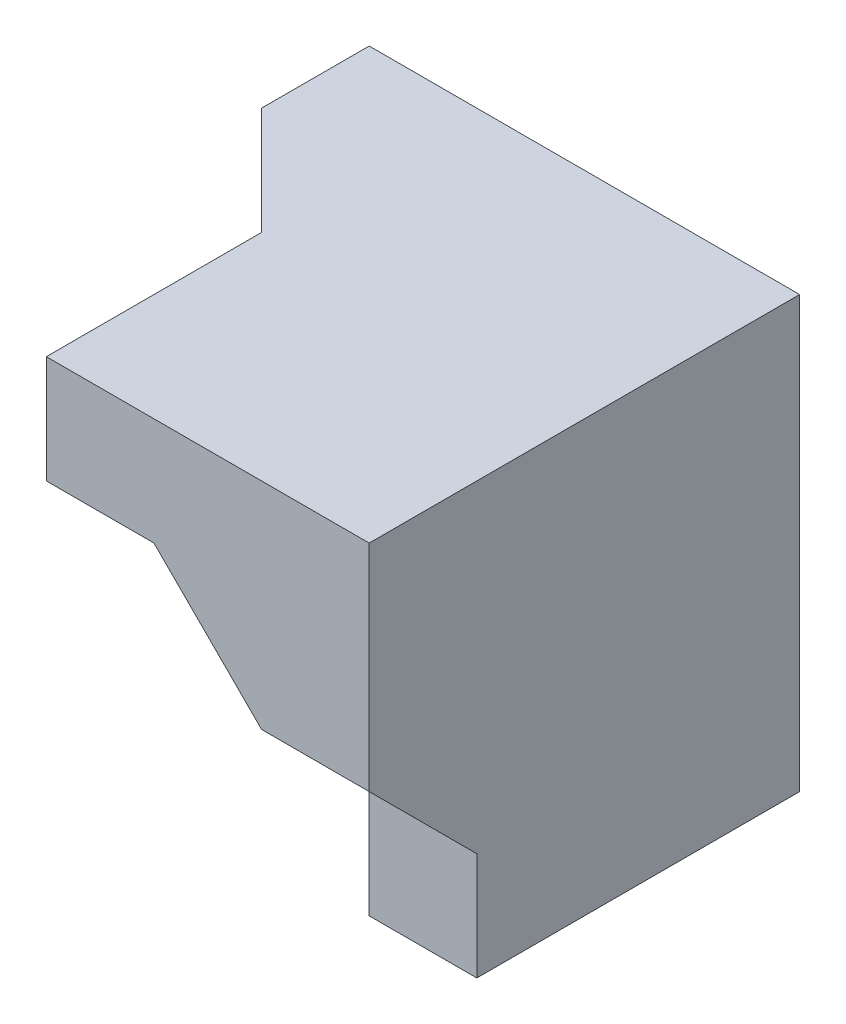
SolidWorks part; units mm, degrees
ref_plane "Front Plane" through (0, 0, 0) normal (0, 0, 1) x (1, 0, 0)
ref_plane "Top Plane" through (0, 0, 0) normal (0, 1, 0) x (1, 0, 0)
ref_plane "Right Plane" through (0, 0, 0) normal (1, 0, 0) x (0, 0, -1)
sketch "Sketch1" plane through (0, 0, 0) normal (0, 0, 1) x (1, 0, 0)
  line L1 (0, 0) -> (40, 0)
  line L2 (0, 0) -> (0, 40)
  line L3 (0, 40) -> (40, 40)
  line L4 (40, 0) -> (40, 40)
  dimension "D1" = 40
  dimension "D2" = 40
extrude "Boss-Extrude1" add sketch "Sketch1" along normal blind 20
sketch "Sketch2" plane through (40, 0, 0) normal (1, 0, 0) x (0, 0, -1)
  line L0 (-20, 0) -> (-30, 0)
  line L1 (-30, 0) -> (-30, 10)
  line L2 (-30, 10) -> (-20, 0)
  line L3 (-20, 0) -> (-20, 10)
  line L4 (-20, 0) -> (-20, 40) construction
  line L5 (-30, 10) -> (-20, 10)
  dimension "D1" = 10
  dimension "D2" = 10
extrude "Boss-Extrude3" add sketch "Sketch2" against normal blind 10 separate body contours L2 L1 L0
sketch "Sketch3" plane through (40, 0, 0) normal (1, 0, 0) x (0, 0, -1)
  line L0 (-20, 0) -> (-20, 10)
  line L1 (-20, 40) -> (-30, 40)
  line L2 (-20, 40) -> (-20, 10)
  line L3 (-20, 10) -> (-30, 10)
  line L4 (-30, 40) -> (-30, 10)
  line L5 (-20, 10) -> (-30, 10)
  line L6 (-30, 10) -> (-20, 0)
  line M3 (-20, 40) -> (-20, 0)
extrude "Boss-Extrude5" add sketch "Sketch3" against normal blind 10 contours L1 L4 L3 M3
sketch "Sketch4" plane through (40, 0, 0) normal (1, 0, 0) x (0, 0, -1)
  line L0 (-20, 0) -> (-20, 10)
  line L1 (-20, 10) -> (-30, 10)
  line L2 (-30, 10) -> (-20, 0)
extrude "Boss-Extrude6" add sketch "Sketch4" against normal blind 10
sketch "Sketch5" plane through (0, 0, 20) normal (0, 0, 1) x (1, 0, 0)
  line L0 (0, 0) -> (30, 0) construction
  line L1 (0, 40) -> (10, 40)
  line L2 (0, 40) -> (0, 0)
  line L3 (0, 0) -> (10, 0)
  line L4 (10, 40) -> (10, 0)
  dimension "D1" = 10
extrude "Cut-Extrude3" cut sketch "Sketch5" against normal blind 25
sketch "Sketch7" plane through (0, 0, 20) normal (0, 0, 1) x (1, 0, 0)
  line L0 (10, 10) -> (20, 0)
  line L1 (10, 0) -> (10, 40) construction
  line L2 (10, 0) -> (30, 0) construction
  line L3 (20, 0) -> (10, 0)
  line L4 (10, 0) -> (10, 10)
  dimension "D1" = 10
  dimension "D2" = 10
extrude "Cut-Extrude4" cut sketch "Sketch7" against normal blind 25
sketch "Sketch8" plane through (0, 0, 20) normal (0, 0, 1) x (1, 0, 0)
  line L0 (30, 0) -> (10, 20)
  line L1 (10, 10) -> (10, 40) construction
  line L2 (10, 20) -> (10, 10)
  line L3 (10, 10) -> (20, 0)
  line L4 (20, 0) -> (30, 0)
  dimension "D1" = 20
extrude "Cut-Extrude5" cut sketch "Sketch8" against normal blind 10
sketch "Sketch9" plane through (10, 0, 0) normal (-1, 0, 0) x (0, 0, 1)
  line L0 (0, 40) -> (0, 10) construction
  line L1 (20, 40) -> (0, 40)
  line L2 (20, 40) -> (20, 20)
  line L3 (20, 20) -> (0, 20)
  line L4 (0, 40) -> (0, 20)
  dimension "D1" = 20
extrude "Boss-Extrude7" add sketch "Sketch9" along normal blind 10
sketch "Sketch10" plane through (0, 40, 0) normal (0, 1, 0) x (1, 0, 0)
  line L0 (10, -20) -> (0, -10)
  line L1 (30, -20) -> (0, -20) construction
  line L2 (0, -20) -> (0, 0) construction
  line L3 (0, -10) -> (0, -20)
  line L4 (0, -20) -> (10, -20)
  dimension "D1" = 10
  dimension "D2" = 10
extrude "Cut-Extrude6" cut sketch "Sketch10" against normal blind 10
sketch "Sketch11" plane through (30, 0, 0) normal (-1, 0, 0) x (0, 0, 1)
  line L0 (30, 10) -> (40, 20)
  line L1 (30, 0) -> (30, 40) construction
  line L2 (40, 20) -> (40, 40)
  line L3 (40, 40) -> (30, 40)
  line L8 (30, 0) -> (30, 40)
  line L9 (30, 40) -> (20, 40)
  line L10 (20, 40) -> (20, 0)
  line L11 (20, 0) -> (30, 0)
  line L12 (30, 10) -> (30, 40)
  dimension "D1" = 10
  dimension "D2" = 10
  dimension "D3" = 10
  dimension "D4" = 0
extrude "Boss-Extrude8" add sketch "Sketch11" against normal blind 10
sketch "Sketch12" plane through (30, 0, 0) normal (-1, 0, 0) x (0, 0, 1)
  line L0 (20, 0) -> (20, 40) construction
  line L1 (40, 40) -> (20, 40)
  line L2 (40, 40) -> (40, 30)
  line L3 (40, 30) -> (20, 30)
  line L4 (20, 40) -> (20, 30)
  dimension "D1" = 10
extrude "Boss-Extrude9" add sketch "Sketch12" along normal blind 20
sketch "Sketch13" plane through (0, 0, 40) normal (0, 0, 1) x (1, 0, 0)
  line L0 (30, 20) -> (20, 30)
  line L1 (10, 30) -> (30, 30) construction
  line L2 (30, 20) -> (30, 30)
  line L3 (30, 30) -> (20, 30)
  dimension "D1" = 10
extrude "Boss-Extrude10" add sketch "Sketch13" against normal blind 20
sketch "Sketch15" plane through (0, 0, 20) normal (0, 0, 1) x (1, 0, 0)
  line L0 (30, 0) -> (10, 20)
sketch "Sketch16" plane through (10, 0, 0) normal (-1, 0, 0) x (0, 0, 1)
  line L0 (20, 20) -> (30, 30)
  line L1 (20, 30) -> (40, 30) construction
  line L2 (30, 30) -> (20, 30)
  line L3 (20, 30) -> (20, 20)
  dimension "D1" = 10
extrude "Boss-Extrude11" add sketch "Sketch16" against normal blind 20
ref_plane "Plane1" through (3.3333, 3.3333, -3.3333) normal (0.5774, 0.5774, -0.5774) x (-0.8165, 0.4082, -0.4082)
sketch "Sketch17" plane through (3.3333, 3.3333, -3.3333) normal (0.5774, 0.5774, -0.5774) x (-0.8165, 0.4082, -0.4082)
  line L0 (-32.6599, 42.4264) -> (-20.4124, 49.4975)
  line L1 (-20.4124, 49.4975) -> (-8.165, 42.4264)
  line L2 (-8.165, 42.4264) -> (-8.165, 28.2843)
  line L3 (-8.165, 28.2843) -> (-32.6599, 14.1421)
  line L4 (-32.6599, 14.1421) -> (-32.6599, 42.4264)
extrude "Boss-Extrude12" add sketch "Sketch17" along normal blind 17
